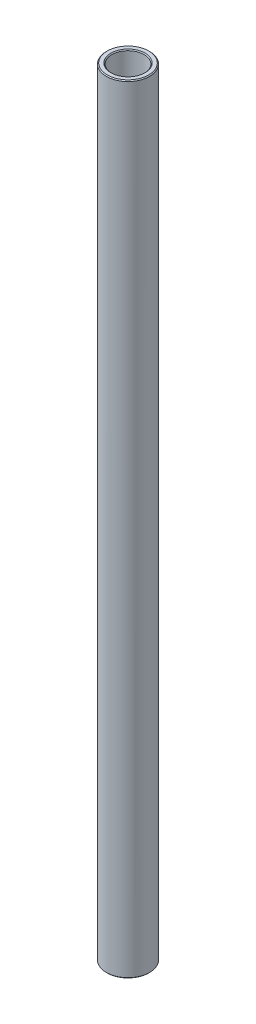
SolidWorks part; units mm, degrees
ref_plane "Front Plane" through (0, 0, 0) normal (0, 0, 1) x (1, 0, 0)
ref_plane "Top Plane" through (0, 0, 0) normal (0, 1, 0) x (1, 0, 0)
ref_plane "Right Plane" through (0, 0, 0) normal (1, 0, 0) x (0, 0, -1)
sketch "Sketch1" plane through (0, 0, 0) normal (0, 0, 1) x (1, 0, 0)
  line L0 (0, 11.6086) -> (0, -11.6086) construction
  line L1 (4.7625, 114.3) -> (6.35, 114.3)
  line L2 (6.35, 114.3) -> (6.35, -114.3)
  line L3 (6.35, -114.3) -> (4.7625, -114.3)
  line L4 (4.7625, -114.3) -> (4.7625, 114.3)
  line L5 (4.7625, 0) -> (0, 0) construction
  dimension "D1" = 9.525
  dimension "D2" = 12.7
  dimension "D3" = 228.6
revolve "Revolve1" add sketch "Sketch1" angle 360 about L0
chamfer "Chamfer1" distance 0.254 angle 45 4 edges at (-4.7625, -114.3, 0) (-6.35, -114.3, 0) (-6.35, 114.3, 0) (-4.7625, 114.3, 0)
